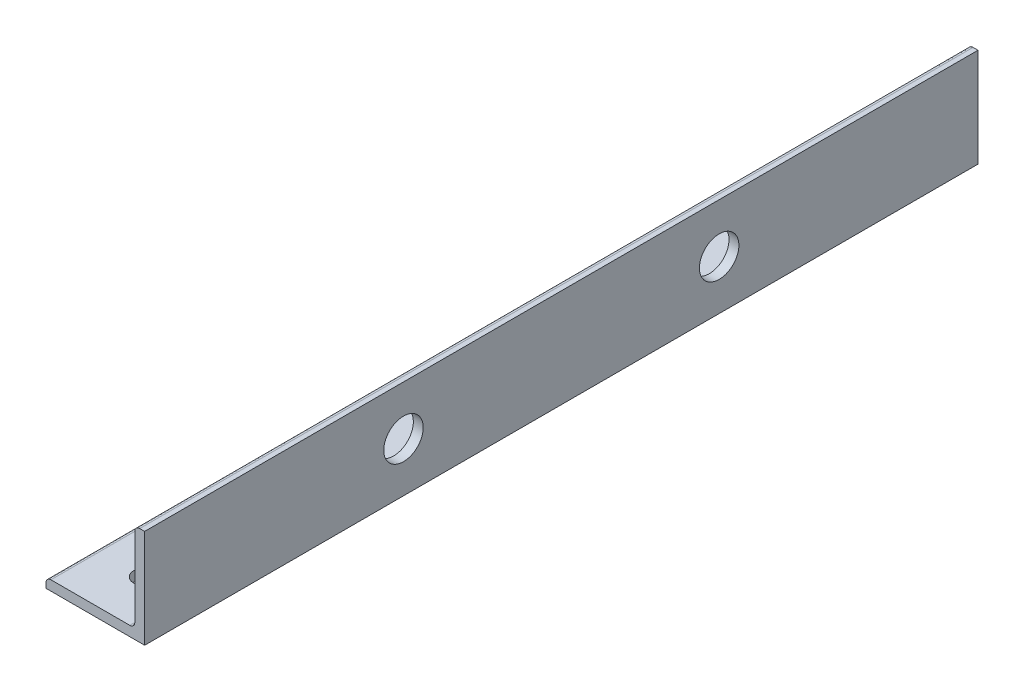
SolidWorks part; units mm, degrees
ref_plane "Front Plane" through (0, 0, 0) normal (0, 0, 1) x (1, 0, 0)
ref_plane "Top Plane" through (0, 0, 0) normal (0, 1, 0) x (1, 0, 0)
ref_plane "Right Plane" through (0, 0, 0) normal (1, 0, 0) x (0, 0, -1)
sketch "Sketch2" plane through (0, 0, 0) normal (0, 0, 1) x (1, 0, 0)
  line L0 (-7.9375, 0) -> (7.9375, 0)
  line L1 (7.9375, 0) -> (7.9375, 15.875)
  line L2 (7.9375, 15.875) -> (6.35, 15.875) construction
  line L3 (6.35, 15.0813) -> (6.35, 2.3812)
  line L4 (5.5563, 1.5875) -> (-7.1438, 1.5875)
  line L5 (-7.9375, 0) -> (-7.9375, 1.5875) construction
  line L6 (7.1438, 15.875) -> (7.9375, 15.875)
  line L7 (-7.9375, 0.7937) -> (-7.9375, 0)
  arc A0 (6.35, 15.0813) -> (7.1438, 15.875) centre (7.1438, 15.0813) cw
  arc A1 (-7.9375, 0.7937) -> (-7.1438, 1.5875) centre (-7.1438, 0.7937) cw
  arc A2 (6.35, 2.3812) -> (5.5563, 1.5875) centre (5.5563, 2.3812) cw
  dimension "Vert" = 15.875
  dimension "Horz" = 15.875
  dimension "Thickness" = 1.5875
extrude "Boss-Extrude1" add sketch "Sketch2" along normal mid plane 134.112
ref_plane "Contact Plane 1" through (0, 1.5875, 0) normal (0, 1, 0) x (1, 0, 0)
ref_plane "Contact Plane 2" through (6.35, 0, 0) normal (-1, 0, 0) x (0, 0, 1)
sketch "Sketch3" plane through (7.9375, 0, 0) normal (1, 0, 0) x (0, 0, -1)
  line L0 (25.4, 7.9375) -> (-25.4, 7.9375)
  line L1 (-67.056, 15.875) -> (67.056, 15.875) construction
  line L2 (-67.056, 15.875) -> (-67.056, 0) construction
  line L3 (-67.056, 0) -> (67.056, 0) construction
  line L4 (67.056, 15.875) -> (67.056, 0) construction
  circle A0 centre (-25.4, 7.9375) radius 3.175
  circle A1 centre (25.4, 7.9375) radius 3.175
  point P6 (67.056, 7.9375)
  point P10 (0, 15.875)
  point P13 (0, 7.9375)
  dimension "D1" = 6.35
  dimension "D2" = 50.8
extrude "Cut-Extrude1" cut sketch "Sketch3" against normal through all
sketch "Sketch4" plane through (0, 0, 0) normal (0, -1, 0) x (1, 0, 0)
  line L0 (0, 59.1185) -> (0, -59.1185)
  line L1 (-7.9375, -67.056) -> (7.9375, -67.056) construction
  line L3 (7.9375, 67.056) -> (7.9375, -67.056) construction
  line L4 (0, 59.1185) -> (7.9375, 59.1185)
  line L5 (7.9375, 59.1185) -> (0, 59.1185)
  line L6 (0, 59.1185) -> (0, 67.056)
  line L7 (-7.9375, 67.056) -> (7.9375, 67.056) construction
  circle A0 centre (0, -59.1185) radius 1.75
  circle A1 centre (0, 59.1185) radius 1.75
  point P4 (0, 0)
  point P9 (0, -67.056)
  point P14 (7.9375, 0)
  dimension "D1" = 3.5
extrude "Cut-Extrude2" cut sketch "Sketch4" against normal through all
